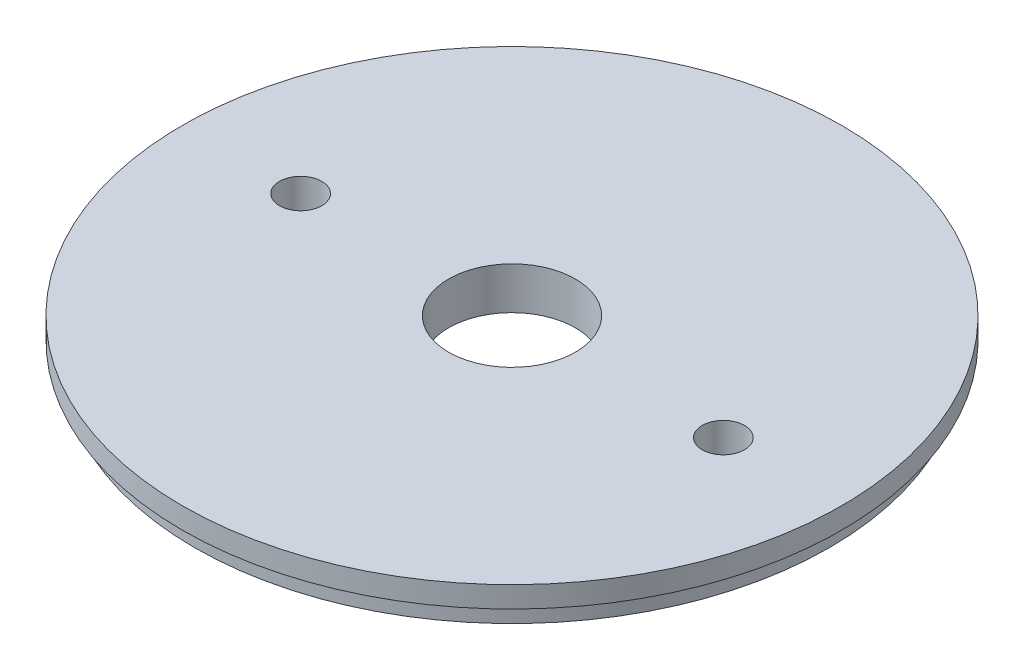
SolidWorks part; units mm, degrees
ref_plane "Front Plane" through (0, 0, 0) normal (0, 0, 1) x (1, 0, 0)
ref_plane "Top Plane" through (0, 0, 0) normal (0, 1, 0) x (1, 0, 0)
ref_plane "Right Plane" through (0, 0, 0) normal (1, 0, 0) x (0, 0, -1)
sketch "Sketch1" plane through (0, 0, 0) normal (0, 1, 0) x (1, 0, 0)
  circle A0 centre (0, 0) radius 47.6885
  dimension "D1" = 95.377
extrude "Boss-Extrude1" add sketch "Sketch1" along normal blind 3.175
sketch "Sketch2" plane through (0, 3.175, 0) normal (0, 1, 0) x (1, 0, 0)
  circle A0 centre (0, 0) radius 49.5046
  dimension "D1" = 99.0092
extrude "Boss-Extrude2" add sketch "Sketch2" along normal blind 3.175
sketch "Sketch3" plane through (0, 6.35, 0) normal (0, 1, 0) x (1, 0, 0)
  circle A0 centre (-31.75, 0) radius 3.175
  circle A1 centre (31.75, 0) radius 3.175
  circle A2 centre (0, 0) radius 9.525
  dimension "D1" = 6.35
  dimension "D2" = 6.35
  dimension "D3" = 19.05
  dimension "D4" = 63.5
  dimension "D5" = 31.75
extrude "Cut-Extrude1" cut sketch "Sketch3" against normal through all
